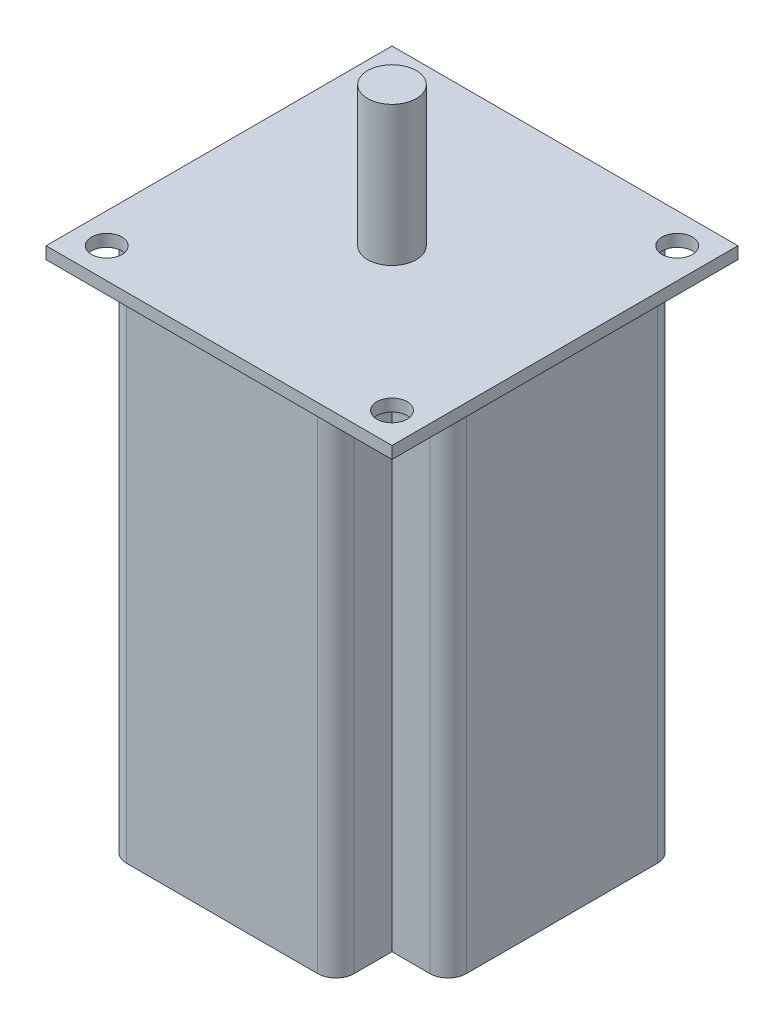
SolidWorks part; units mm, degrees
ref_plane "前视基准面" through (0, 0, 0) normal (0, 0, 1) x (1, 0, 0)
ref_plane "上视基准面" through (0, 0, 0) normal (0, 1, 0) x (1, 0, 0)
ref_plane "右视基准面" through (0, 0, 0) normal (1, 0, 0) x (0, 0, -1)
sketch "草图1" plane through (0, 0, 0) normal (0, 1, 0) x (1, 0, 0)
  line L1 (-25, 18.75) -> (25, 18.75)
  line L2 (-28, 15.75) -> (-28, -15.75)
  line L3 (-25, -18.75) -> (25, -18.75)
  line L4 (28, 15.75) -> (28, -15.75)
  line L5 (-28, 18.75) -> (28, -18.75) construction
  line L6 (-28, -18.75) -> (28, 18.75) construction
  line L7 (-15.75, 28) -> (15.75, 28)
  line L8 (-18.75, 25) -> (-18.75, -25)
  line L9 (-15.75, -28) -> (15.75, -28)
  line L10 (18.75, 25) -> (18.75, -25)
  line L11 (-18.75, 28) -> (18.75, -28) construction
  line L12 (-18.75, -28) -> (18.75, 28) construction
  arc A0 (18.75, 25) -> (15.75, 28) centre (15.75, 25) ccw
  arc A1 (-15.75, 28) -> (-18.75, 25) centre (-15.75, 25) ccw
  arc A2 (-15.75, -28) -> (-18.75, -25) centre (-15.75, -25) cw
  arc A3 (15.75, -28) -> (18.75, -25) centre (15.75, -25) ccw
  arc A4 (-28, -15.75) -> (-25, -18.75) centre (-25, -15.75) ccw
  arc A5 (28, -15.75) -> (25, -18.75) centre (25, -15.75) cw
  arc A6 (28, 15.75) -> (25, 18.75) centre (25, 15.75) ccw
  arc A7 (-28, 15.75) -> (-25, 18.75) centre (-25, 15.75) cw
  point P0 (0, 0)
  point P6 (0, 0)
  dimension "D5" = 3
  dimension "D1" = 56
  dimension "D2" = 37.5
  dimension "D3" = 56
  dimension "D4" = 37.5
extrude "凸台-拉伸1" add sketch "草图1" along normal blind 82 contours A7 L2 A4 L3 L8 L1 | L10 L1 L8 L3 | L4 A6 L1 L10 L3 A5 | L9 A3 L10 L3 L8 A2 | L7 A1 L8 L1 L10 A0
ref_plane "基准面1" through (0, 82, 0) normal (0, 1, 0) x (1, 0, 0)
sketch "草图2" plane through (0, 82, 0) normal (0, 1, 0) x (1, 0, 0)
  line L1 (-28.5, 28.5) -> (28.5, 28.5)
  line L2 (-28.5, 28.5) -> (-28.5, -28.5)
  line L3 (-28.5, -28.5) -> (28.5, -28.5)
  line L4 (28.5, 28.5) -> (28.5, -28.5)
  line L5 (-28.5, 28.5) -> (28.5, -28.5) construction
  line L6 (-28.5, -28.5) -> (28.5, 28.5) construction
  point P0 (0, 0)
  dimension "D1" = 57
  dimension "D2" = 57
extrude "凸台-拉伸2" add sketch "草图2" against normal blind 2
sketch "草图3" plane through (0, 82, 0) normal (0, 1, 0) x (1, 0, 0)
  line L1 (-23.5, 23.5) -> (23.5, 23.5) construction
  line L2 (-23.5, 23.5) -> (-23.5, -23.5) construction
  line L3 (-23.5, -23.5) -> (23.5, -23.5) construction
  line L4 (23.5, 23.5) -> (23.5, -23.5) construction
  line L5 (-23.5, 23.5) -> (23.5, -23.5) construction
  line L6 (-23.5, -23.5) -> (23.5, 23.5) construction
  circle A0 centre (23.5, 23.5) radius 2.5
  circle A1 centre (-23.5, 23.5) radius 2.5
  circle A2 centre (-23.5, -23.5) radius 2.5
  circle A3 centre (23.5, -23.5) radius 2.5
  point P0 (0, 0)
  dimension "D3" = 5
  dimension "D4" = 5
  dimension "D5" = 5
  dimension "D6" = 5
  dimension "D1" = 47
  dimension "D2" = 47
extrude "切除-拉伸1" cut sketch "草图3" against normal blind 2
sketch "草图4" plane through (0, 82, 0) normal (0, 1, 0) x (1, 0, 0)
  circle A0 centre (0, 0) radius 4
  dimension "D1" = 8
extrude "凸台-拉伸3" add sketch "草图4" along normal blind 23
